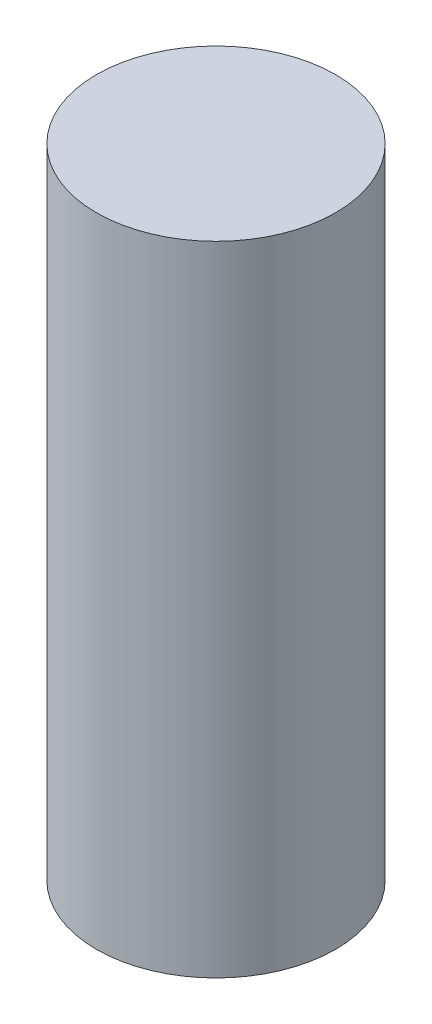
SolidWorks part; units mm, degrees
ref_plane "Front Plane" through (0, 0, 0) normal (0, 0, 1) x (1, 0, 0)
ref_plane "Top Plane" through (0, 0, 0) normal (0, 1, 0) x (1, 0, 0)
ref_plane "Right Plane" through (0, 0, 0) normal (1, 0, 0) x (0, 0, -1)
sketch "Sketch1" plane through (0, 0, 0) normal (0, 1, 0) x (1, 0, 0)
  circle A0 centre (0, 0) radius 4.7625
  dimension "D1" = 9.525
extrude "Boss-Extrude1" add sketch "Sketch1" along normal blind 25.4
